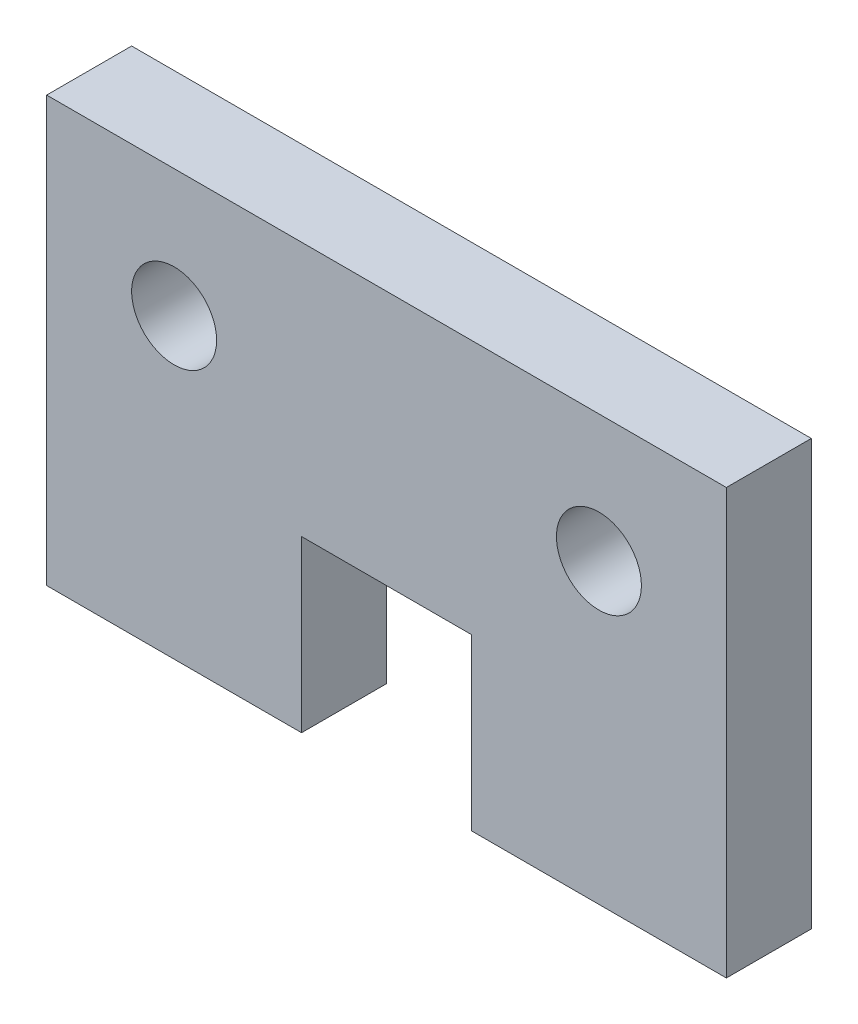
SolidWorks part; units mm, degrees
ref_plane "Front Plane" through (0, 0, 0) normal (0, 0, 1) x (1, 0, 0)
ref_plane "Top Plane" through (0, 0, 0) normal (0, 1, 0) x (1, 0, 0)
ref_plane "Right Plane" through (0, 0, 0) normal (1, 0, 0) x (0, 0, -1)
sketch "Sketch1" plane through (0, 0, 0) normal (0, 0, 1) x (1, 0, 0)
  line L0 (-46.2531, 46.2531) -> (-46.2531, -17.2469)
  line L1 (-46.2531, -17.2469) -> (-8.1531, -17.2469)
  line L2 (-8.1531, -17.2469) -> (-8.1531, 8.1531)
  line L3 (-8.1531, 8.1531) -> (17.2469, 8.1531)
  line L4 (17.2469, 8.1531) -> (17.2469, -17.2469)
  line L5 (17.2469, -17.2469) -> (55.3469, -17.2469)
  line L6 (55.3469, -17.2469) -> (55.3469, 46.2531)
  line L7 (55.3469, 46.2531) -> (-46.2531, 46.2531)
  circle A0 centre (-27.2031, 27.2031) radius 6.35
  circle A1 centre (36.2969, 27.2031) radius 6.35
  dimension "D7" = 12.7
  dimension "D8" = 19.05
  dimension "D9" = 19.05
  dimension "D10" = 2
  dimension "D11" = 63.5
  dimension "D1" = 101.6
  dimension "D2" = 38.1
  dimension "D3" = 38.1
  dimension "D4" = 63.5
  dimension "D5" = 63.5
  dimension "D6" = 25.4
extrude "Boss-Extrude1" add sketch "Sketch1" along normal blind 12.7
